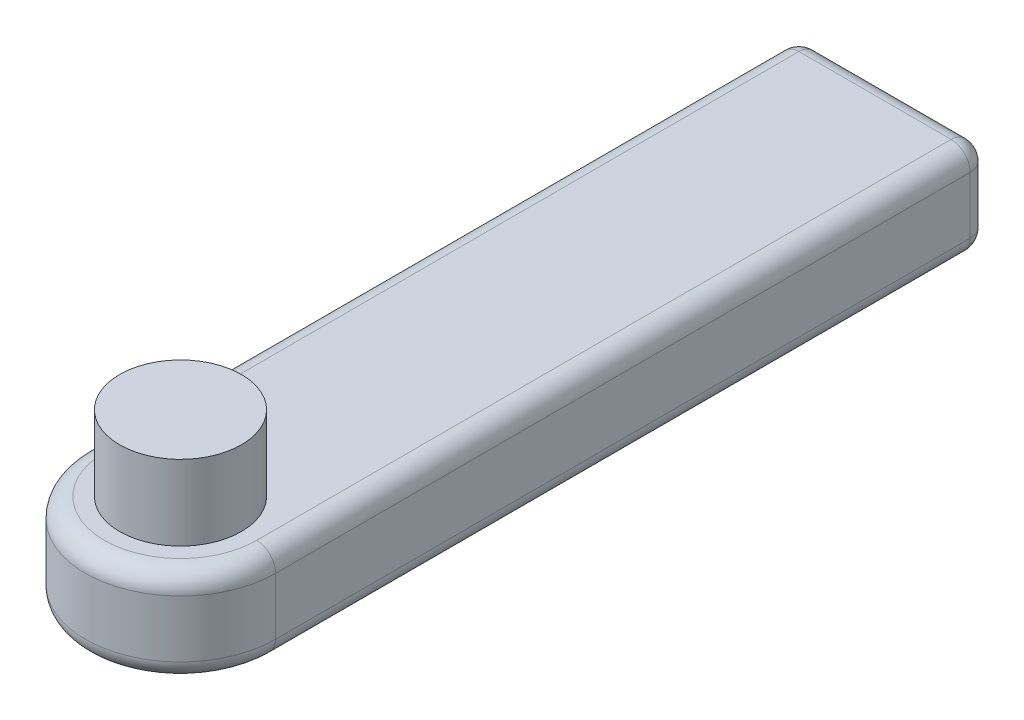
SolidWorks part; units mm, degrees
ref_plane "Front Plane" through (0, 0, 0) normal (0, 0, 1) x (1, 0, 0)
ref_plane "Top Plane" through (0, 0, 0) normal (0, 1, 0) x (1, 0, 0)
ref_plane "Right Plane" through (0, 0, 0) normal (1, 0, 0) x (0, 0, -1)
sketch "Sketch2" plane through (0, 0, 0) normal (0, 1, 0) x (1, 0, 0)
  line L0 (-10, 0) -> (-10, 75)
  line L1 (10, 0) -> (10, 75)
  line L2 (-10, 75) -> (10, 75)
  circle A0 centre (0, 0) radius 10
  dimension "D1" = 20
  dimension "D2" = 75
extrude "Boss-Extrude2" add sketch "Sketch2" along normal blind 10 contours A0 | A0 L1 L2 L0
sketch "Sketch3" plane through (0, 10, 0) normal (0, 1, 0) x (1, 0, 0)
  circle A0 centre (0, 0) radius 6.4
  dimension "D1" = 12.8
extrude "Boss-Extrude3" add sketch "Sketch3" along normal blind 7.9
sketch "Sketch4" plane through (0, 0, -75) normal (0, 0, -1) x (-1, 0, 0)
  line L0 (0, 10) -> (0, 0) construction
  line L1 (10, 10) -> (-10, 10) construction
  line L2 (-10, 5) -> (10, 5) construction
  line L3 (-10, 10) -> (-10, 0) construction
  line L4 (10, 10) -> (10, 0) construction
  circle A1 centre (0, 5) radius 2.75
  dimension "D2" = 5.5
extrude "Cut-Extrude1" cut sketch "Sketch4" against normal blind 5
fillet "Fillet1" radius 2 10 edges at (-10, 0, -37.5) (-10, 10, -37.5) (10, 0, -37.5) (10, 10, -37.5) (0, 0, 10) (0, 10, 10) (10, 5, -75) (0, 0, -75) (0, 10, -75) (-10, 5, -75)
sketch "Sketch6" plane through (0, 0, -75) normal (0, 0, -1) x (-1, 0, 0)
  line L0 (-10, 5) -> (10, 5) construction
  line L1 (-10, 2) -> (-10, 8) construction
  line L2 (10, 8) -> (10, 2) construction
